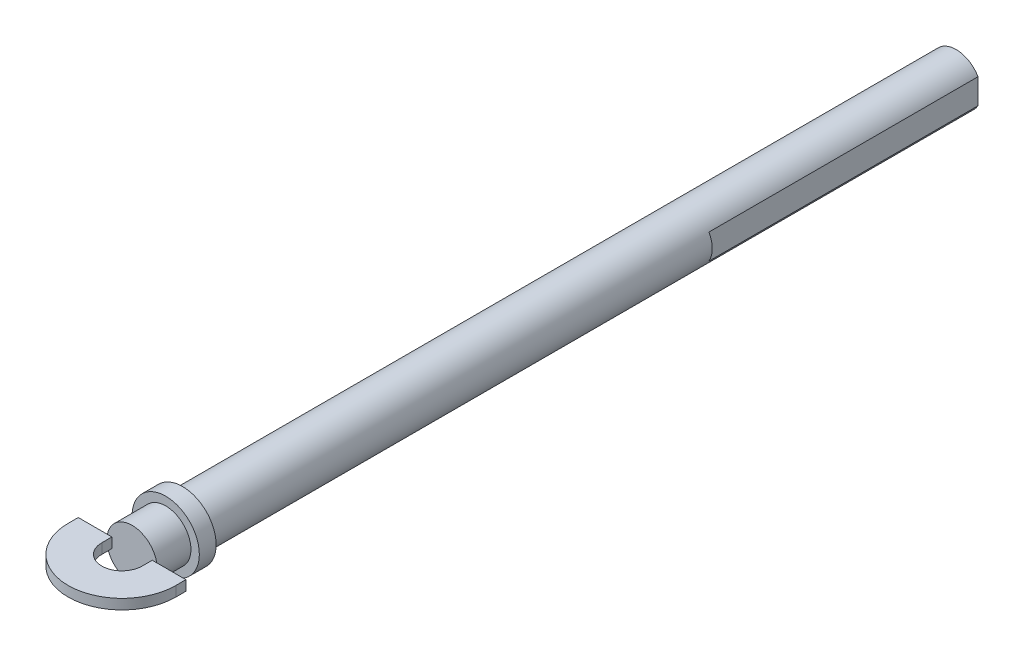
SolidWorks part; units mm, degrees
ref_plane "Front Plane" through (0, 0, 0) normal (0, 0, 1) x (1, 0, 0)
ref_plane "Top Plane" through (0, 0, 0) normal (0, 1, 0) x (1, 0, 0)
ref_plane "Right Plane" through (0, 0, 0) normal (1, 0, 0) x (0, 0, -1)
sketch "Sketch1" plane through (0, 0, 0) normal (0, 0, 1) x (1, 0, 0)
  circle A0 centre (0, 0) radius 7.5
  dimension "D1" = 15
extrude "Boss-Extrude1" add sketch "Sketch1" along normal blind 230
sketch "Sketch2" plane through (0, 0, 230) normal (0, 0, 1) x (1, 0, 0)
  circle A0 centre (0, 0) radius 10
  dimension "D1" = 20
extrude "Boss-Extrude2" add sketch "Sketch2" along normal blind 5
sketch "Sketch3" plane through (0, 0, 235) normal (0, 0, 1) x (1, 0, 0)
  circle A0 centre (0, 0) radius 7.5 construction
  circle A1 centre (0, 0) radius 7.5
extrude "Boss-Extrude3" add sketch "Sketch3" along normal blind 10
sketch "Sketch4" plane through (0, 0, 0) normal (0, 0, -1) x (-1, 0, 0)
  line L0 (-6.5, 3.7417) -> (-6.5, -3.7417)
  line L1 (0, 7.5) -> (0, -7.5) construction
  line L2 (6.5, 3.7417) -> (6.5, -3.7417)
  arc A0 (-6.5, 3.7417) -> (-6.5, -3.7417) centre (0, 0) ccw
  circle A1 centre (0, 0) radius 7.5
  arc A2 (6.5, -3.7417) -> (6.5, 3.7417) centre (0, 0) ccw
  dimension "D2" = 6.5
  dimension "D1" = 0
extrude "Cut-Extrude1" cut sketch "Sketch4" against normal blind 80
sketch "Sketch5" plane through (0, 0, 0) normal (0, 1, 0) x (1, 0, 0)
  line L0 (-6, -245) -> (-6, -248)
  line L1 (-7.5, -245) -> (7.5, -245) construction
  line L2 (6, -248) -> (6, -245)
  line L3 (0, -248) -> (0, -235) construction
  line L4 (-7.5, -235) -> (7.5, -235) construction
  arc A0 (-6, -248) -> (6, -248) centre (0, -248) ccw
  dimension "D2" = 12
  dimension "D1" = 3
extrude "Extrude-Thin1" add sketch "Sketch5" along normal mid plane 3 thin
